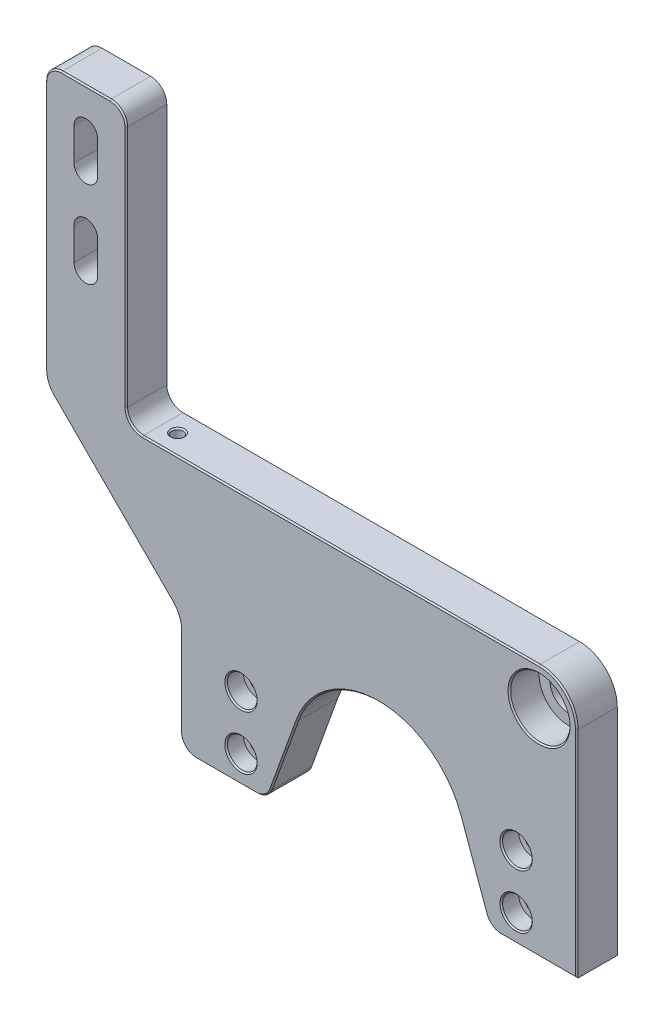
SolidWorks part; units mm, degrees
material "Alumina"
ref_plane "Plan de face" through (0, 0, 0) normal (0, 0, 1) x (1, 0, 0)
ref_plane "Plan de dessus" through (0, 0, 0) normal (0, 1, 0) x (1, 0, 0)
ref_plane "Plan de droite" through (0, 0, 0) normal (1, 0, 0) x (0, 0, -1)
sketch "Sketch1" plane through (0, 0, 0) normal (0, 0, 1) x (1, 0, 0)
  line L0 (-54.0835, -51.5566) -> (92.9165, -51.5566)
  line L1 (-54.0835, -51.5566) -> (-54.0835, -8.5566)
  line L2 (-74.0835, 42.1934) -> (92.9165, 42.1934)
  line L3 (92.9165, -51.5566) -> (92.9165, 42.1934)
  line L4 (-10.6874, -20.7052) -> (-21.8083, -51.5566)
  line L7 (19.4165, -31.5566) -> (19.4165, -41.2485) construction
  line L8 (49.5204, -20.7052) -> (60.6413, -51.5566)
  line L9 (-54.0835, -8.5566) -> (-104.0835, 41.4434)
  line L11 (-74.0835, 42.1934) -> (-74.0835, 144.1934)
  line L12 (-74.0835, 144.1934) -> (-104.0835, 144.1934)
  line L13 (-104.0835, 41.4434) -> (-104.0835, 144.1934)
  line L14 (-89.0835, 129.1934) -> (-89.0835, 117.1934) construction
  line L15 (-84.6835, 129.1934) -> (-84.6835, 117.1934)
  line L16 (-93.4835, 129.1934) -> (-93.4835, 117.1934)
  line L17 (-89.0835, 97.1934) -> (-89.0835, 85.1934) construction
  line L18 (-84.6835, 97.1934) -> (-84.6835, 85.1934)
  line L19 (-93.4835, 97.1934) -> (-93.4835, 85.1934)
  arc A0 (49.5204, -20.7052) -> (-10.6874, -20.7052) centre (19.4165, -31.5566) ccw
  arc A1 (-84.6835, 129.1934) -> (-93.4835, 129.1934) centre (-89.0835, 129.1934) ccw
  arc A2 (-93.4835, 117.1934) -> (-84.6835, 117.1934) centre (-89.0835, 117.1934) ccw
  arc A3 (-84.6835, 97.1934) -> (-93.4835, 97.1934) centre (-89.0835, 97.1934) ccw
  arc A4 (-93.4835, 85.1934) -> (-84.6835, 85.1934) centre (-89.0835, 85.1934) ccw
  point P4 (-89.0835, 144.1934)
  point P16 (-89.0835, 123.1934)
  point P24 (-89.0835, 91.1934)
  dimension "D2" = 64
  dimension "D9" = 4.4
  dimension "D10" = 4.4
  dimension "D1" = 102
  dimension "D3" = 93.75
  dimension "D4" = 167
  dimension "D5" = 30
  dimension "D6" = 45
  dimension "D7" = 12
  dimension "D8" = 12
  dimension "D11" = 15
  dimension "D12" = 32
  dimension "D13" = 21
extrude "Boss-Extrude1" add sketch "Sketch1" along normal blind 15
fillet "Fillet1" radius 6 6 edges at (-21.8083, -51.5566, 7.5) (60.6413, -51.5566, 7.5) (-74.0835, 42.1934, 7.5) (-74.0835, 144.1934, 7.5) (-104.0835, 144.1934, 7.5) (-54.0835, -51.5566, 7.5)
hole_wizard "CBORE for M6 Hex Socket Head Cap Screw1" positions "Sketch3" profile "Sketch4" counterbore size "M6" standard "ISO" end condition through all
sketch "Sketch3" plane through (0, 0, 15) normal (0, 0, 1) x (1, 0, 0)
  line L0 (-54.0835, -45.5566) -> (-54.0835, -8.5566) construction
  line L1 (-48.0835, -51.5566) -> (-26.0234, -51.5566) construction
  line L2 (92.9165, -51.5566) -> (92.9165, 42.1934) construction
  point P0 (-31.5835, -41.5566)
  point P2 (-31.5835, -21.5566)
  point P4 (70.4165, -41.5566)
  point P6 (70.4165, -21.5566)
  dimension "D1" = 20
  dimension "D2" = 22.5
  dimension "D3" = 10
  dimension "D4" = 22.5
sketch "Sketch4" plane through (-31.5835, -41.5566, 15) normal (1, 0, 0) x (0, -1, 0)
  line L0 (0, 0) -> (0, 15)
  line L1 (0, 15) -> (3.3, 15)
  line L3 (3.3, 15) -> (3.3, 6.4)
  line L4 (3.3, 6.4) -> (5.5, 6.4)
  line L5 (5.5, 6.4) -> (5.5, 0)
  line L7 (5.5, 0) -> (0, 0)
  line L11 (0, -6.35) -> (0, 107.95) construction
  dimension "Thru Hole Dia." = 6.6
  dimension "Thru Hole Depth" = 15
  dimension "C'Bore Dia." = 11
  dimension "C'Bore Depth" = 6.4
sketch "Sketch6" plane through (0, 0, 15) normal (0, 0, 1) x (1, 0, 0)
  line L2 (-68.0835, 42.1934) -> (92.9165, 42.1934) construction
  line L3 (92.9165, -51.5566) -> (92.9165, 42.1934) construction
  circle A0 centre (78.9165, 28.1934) radius 7
  dimension "D1" = 14
  dimension "D2" = 14
  dimension "D3" = 14
extrude "Cut-Extrude3" cut sketch "Sketch6" against normal through all
sketch "Sketch7" plane through (0, 0, 15) normal (0, 0, 1) x (1, 0, 0)
  circle A0 centre (78.9165, 28.1934) radius 11
  dimension "D1" = 22
extrude "Cut-Extrude4" cut sketch "Sketch7" against normal blind 11
hole_wizard "Tap Drill for M5 Tap1" positions "Sketch9" profile "Sketch10" hole size "M5" standard "ISO"
sketch "Sketch9" plane through (0, 42.1934, 0) normal (0, 1, 0) x (1, 0, 0)
  line L1 (-68.0835, -15) -> (92.9165, -15) construction
  line L2 (-74.0835, -15) -> (-74.0835, 0) construction
  point P0 (-62.5835, -7.5)
  dimension "D1" = 11.5
  dimension "D2" = 7.5
sketch "Sketch10" plane through (-62.5835, 42.1934, 7.5) normal (1, 0, 0) x (0, 0, 1)
  line L0 (0, 0) -> (0, 11.2618)
  line L1 (0, 11.2618) -> (2.1, 10)
  line L2 (2.1, 10) -> (2.1, 0)
  line L5 (2.1, 0) -> (0, 0)
  line L10 (0, 11.2618) -> (-2.1, 10) construction
  line L11 (0, -6.35) -> (0, 107.95) construction
  dimension "Hole Dia." = 4.2
  dimension "Hole Depth" = 10
  dimension "Drill Angle" = 118
fillet "Fillet4" radius 14 1 edges at (92.9165, 42.1934, 7.5)
fillet "Fillet5" radius 10 2 edges at (-104.0835, 41.4434, 7.5) (-54.0835, -8.5566, 7.5)
chamfer "Chamfer1" distance 0.5 angle 45 27 edges at (-54.0835, -29.1277, 15) (5.4165, 42.1934, 15) (92.9165, -11.6816, 15) (78.8865, -51.5566, 15) (54.3662, -34.1482, 15) (19.4165, 0.4434, 15) (-15.5332, -34.1482, 15) (-22.5743, -50.4662, 15) (-37.0535, -51.5566, 15) (61.4073, -50.4662, 15) (88.816, 38.0929, 15) (75.9165, -41.5566, 15) (-26.0835, -41.5566, 15) (-26.0835, -21.5566, 15) (75.9165, -21.5566, 15) (89.9165, 28.1934, 15) (-62.5835, 42.1934, 9.6) (-72.3261, 43.9507, 15) (-74.0835, 93.1934, 15) (-75.8409, 142.436, 15) (-89.0835, 144.1934, 15) (-102.3261, 142.436, 15) (-104.0835, 91.8895, 15) (-103.3223, 41.7587, 15) (-79.0835, 16.4434, 15) (-54.8447, -8.8719, 15) (-52.3261, -49.7993, 15)
